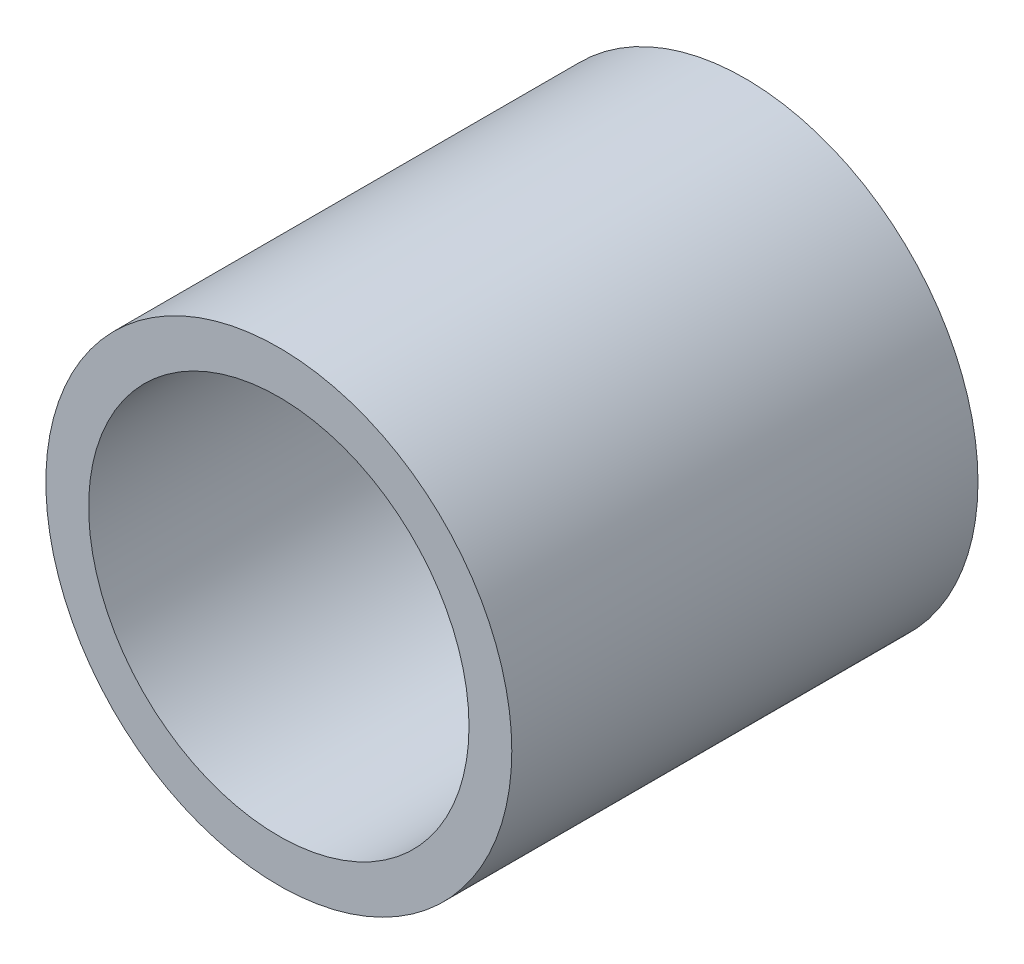
SolidWorks part; units mm, degrees
ref_plane "Ebene vorne" through (0, 0, 0) normal (0, 0, 1) x (1, 0, 0)
ref_plane "Ebene oben" through (0, 0, 0) normal (0, 1, 0) x (1, 0, 0)
ref_plane "Ebene rechts" through (0, 0, 0) normal (1, 0, 0) x (0, 0, -1)
sketch "Skizze1" plane through (0, 0, 0) normal (0, 0, 1) x (1, 0, 0)
  circle A0 centre (0, 0) radius 4.1
  circle A1 centre (0, 0) radius 5.0225
  dimension "D1" = 8.2
  dimension "D2" = 10.045
extrude "Aufsatz-Linear austragen1" add sketch "Skizze1" along normal blind 10.05
